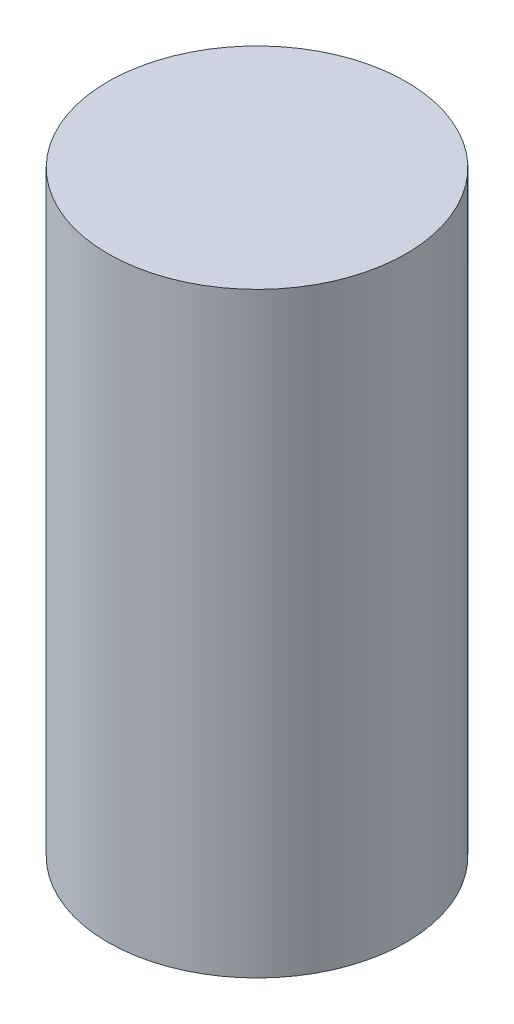
SolidWorks part; units mm, degrees
material "Nickel"
ref_plane "Front Plane" through (0, 0, 0) normal (0, 0, 1) x (1, 0, 0)
ref_plane "Top Plane" through (0, 0, 0) normal (0, 1, 0) x (1, 0, 0)
ref_plane "Right Plane" through (0, 0, 0) normal (1, 0, 0) x (0, 0, -1)
sketch "Sketch1" plane through (0, 0, 0) normal (0, 1, 0) x (1, 0, 0)
  circle A0 centre (0, 0) radius 3.175
  dimension "D1" = 6.35
extrude "Boss-Extrude1" add sketch "Sketch1" along normal blind 12.7
